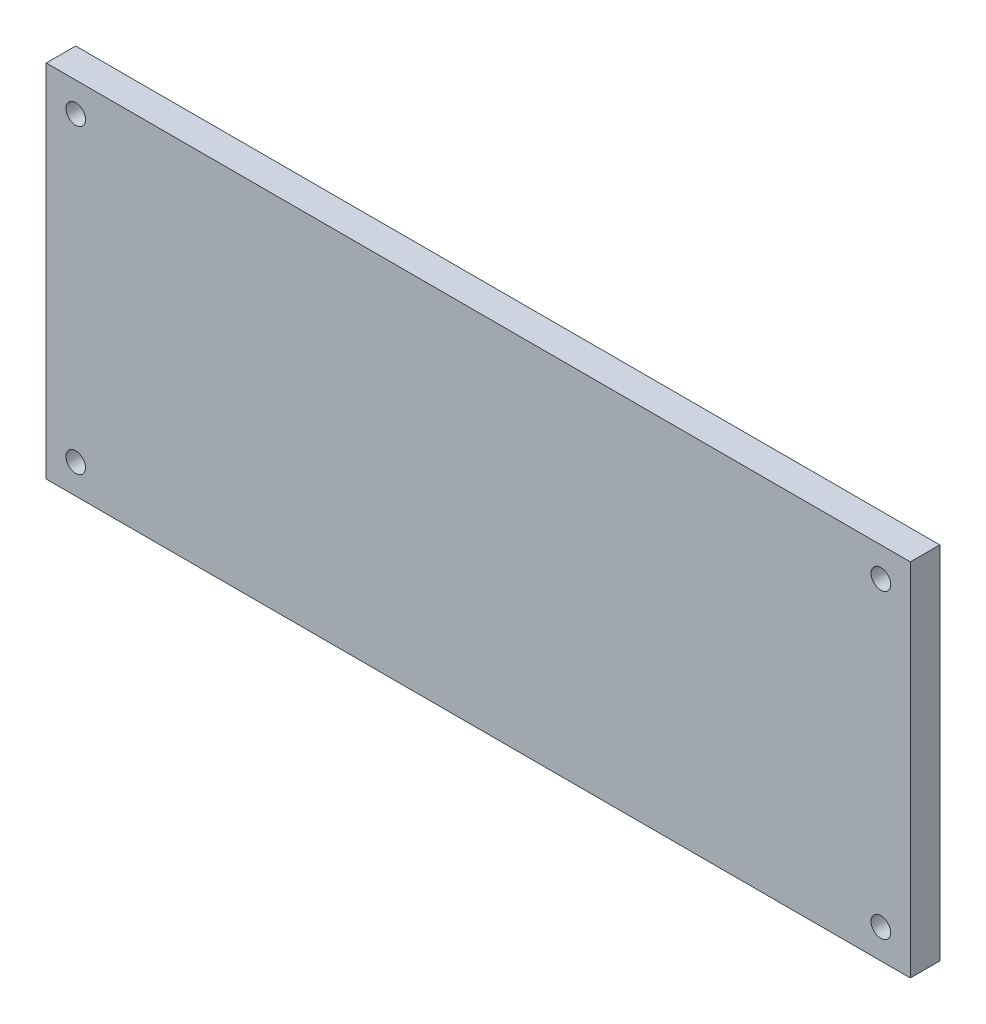
SolidWorks part; units mm, degrees
ref_plane "Спереди" through (0, 0, 0) normal (0, 0, 1) x (1, 0, 0)
ref_plane "Сверху" through (0, 0, 0) normal (0, 1, 0) x (1, 0, 0)
ref_plane "Справа" through (0, 0, 0) normal (1, 0, 0) x (0, 0, -1)
other "Configuration Table"
sketch "Эскиз1" plane through (0, 0, 0) normal (0, 0, 1) x (1, 0, 0)
  line L0 (22, 18.35) -> (22, 0) construction
  line L1 (0, 0) -> (44, 0)
  line L2 (0, 0) -> (0, 18.35)
  line L3 (0, 18.35) -> (44, 18.35)
  line L4 (44, 0) -> (44, 18.35)
  line L5 (0, 9.175) -> (44, 9.175) construction
  circle A0 centre (1.5, 16.85) radius 0.5
  circle A1 centre (42.5, 16.85) radius 0.5
  circle A2 centre (42.5, 1.5) radius 0.5
  circle A3 centre (1.5, 1.5) radius 0.5
  dimension "D3" = 1.5
  dimension "D5" = 1
  dimension "D1" = 18.35
  dimension "D2" = 44
  dimension "D4" = 1.5
extrude "Бобышка-Вытянуть1" add sketch "Эскиз1" along normal blind 1.5
